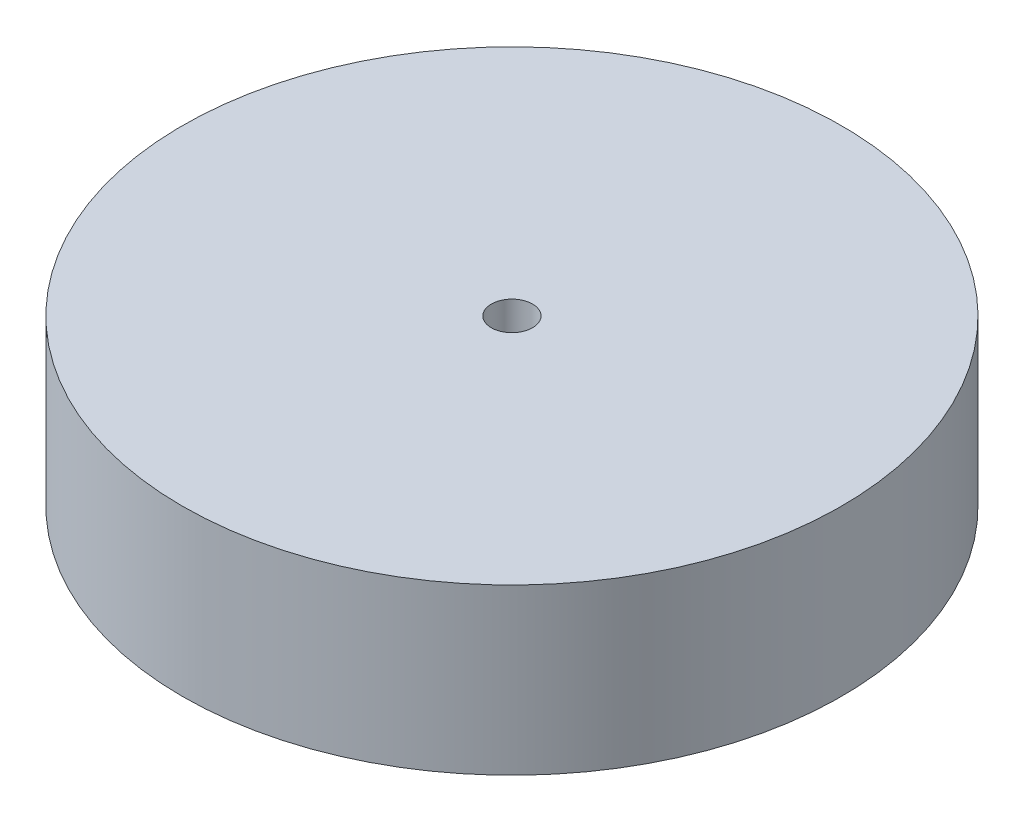
SolidWorks part; units mm, degrees
ref_plane "Front Plane" through (0, 0, 0) normal (0, 0, 1) x (1, 0, 0)
ref_plane "Top Plane" through (0, 0, 0) normal (0, 1, 0) x (1, 0, 0)
ref_plane "Right Plane" through (0, 0, 0) normal (1, 0, 0) x (0, 0, -1)
sketch "Sketch1" plane through (0, 0, 0) normal (0, 1, 0) x (1, 0, 0)
  circle A0 centre (0, 0) radius 50.8
  dimension "D1" = 101.6
extrude "Boss-Extrude1" add sketch "Sketch1" along normal blind 25.4
sketch "Sketch2" plane through (0, 25.4, 0) normal (0, 1, 0) x (1, 0, 0)
  circle A0 centre (0, 0) radius 3.175
  dimension "D1" = 6.35
extrude "Cut-Extrude1" cut sketch "Sketch2" against normal blind 25.4
